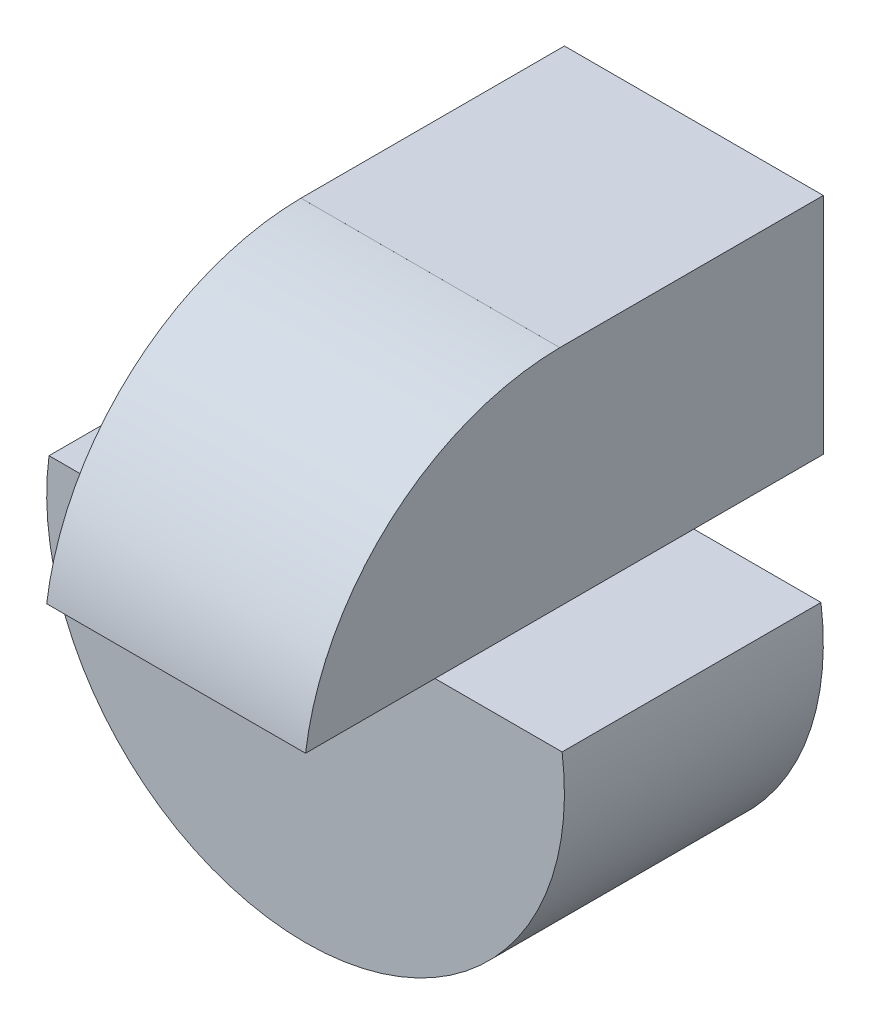
SolidWorks part; units mm, degrees
ref_plane "Front Plane" through (0, 0, 0) normal (0, 0, 1) x (1, 0, 0)
ref_plane "Top Plane" through (0, 0, 0) normal (0, 1, 0) x (1, 0, 0)
ref_plane "Right Plane" through (0, 0, 0) normal (1, 0, 0) x (0, 0, -1)
sketch "Sketch1" plane through (0, 0, 0) normal (0, 0, 1) x (1, 0, 0)
  line L1 (0, 0) -> (40, 0)
  line L2 (0, 0) -> (0, 40)
  line L3 (0, 40) -> (40, 40)
  line L4 (40, 0) -> (40, 40)
  dimension "D1" = 40
  dimension "D2" = 40
extrude "Boss-Extrude1" add sketch "Sketch1" along normal blind 40
sketch "Sketch2" plane through (0, 0, 40) normal (0, 0, 1) x (1, 0, 0)
  line L0 (0, 0) -> (40, 0) construction
  line L1 (0, 40) -> (10, 40)
  line L2 (0, 40) -> (0, 20)
  line L3 (0, 20) -> (10, 20)
  line L4 (10, 40) -> (10, 20)
  line L5 (40, 40) -> (30, 40)
  line L6 (40, 40) -> (40, 20)
  line L7 (40, 20) -> (30, 20)
  line L8 (30, 40) -> (30, 20)
  line L9 (0, 20) -> (0, 0)
  line L10 (0, 0) -> (40, 0)
  line L11 (40, 0) -> (40, 20)
  arc A0 (20, 0) -> (40, 20) centre (20, 20) ccw
  arc A1 (20, 0) -> (0, 20) centre (20, 20) cw
  line M1 (0, 40) -> (0, 0)
  line M2 (0, 0) -> (40, 0)
  line M3 (40, 0) -> (40, 40)
  line M4 (40, 40) -> (0, 40)
  dimension "D5" = 20
  dimension "D6" = 20
  dimension "D1" = 10
  dimension "D2" = 10
  dimension "D3" = 20
  dimension "D4" = 20
extrude "Cut-Extrude1" cut sketch "Sketch2" against normal blind 40 contours A1 M2 M1 | A0 L10 M3 | L8 L7 M4 M3 | L4 L3 M4 M1
sketch "Sketch3" plane through (0, 20, 0) normal (0, 1, 0) x (1, 0, 0)
  line L0 (10, 0) -> (10, -40) construction
  line L1 (0, 0) -> (10, 0)
  line L2 (0, 0) -> (0, -10)
  line L3 (0, -10) -> (10, -10)
  line L4 (10, 0) -> (10, -10)
  line L5 (30, 0) -> (30, -40) construction
  line L6 (40, 0) -> (30, 0)
  line L7 (40, 0) -> (40, -10)
  line L8 (40, -10) -> (30, -10)
  line L9 (30, 0) -> (30, -10)
  line L11 (40, -40) -> (30, -40)
  line L12 (40, -40) -> (40, -30)
  line L13 (40, -30) -> (30, -30)
  line L14 (30, -40) -> (30, -30)
  line L15 (0, -40) -> (10, -40)
  line L16 (0, -40) -> (0, -30)
  line L17 (0, -30) -> (10, -30)
  line L18 (10, -40) -> (10, -30)
  dimension "D1" = 10
  dimension "D2" = 10
  dimension "D3" = 10
  dimension "D4" = 10
extrude "Cut-Extrude2" cut sketch "Sketch3" against normal blind 40
sketch "Sketch4" plane through (10, 0, 0) normal (-1, 0, 0) x (0, 0, 1)
  line L0 (0, 22.6795) -> (10, 22.6795)
  line L1 (0, 2.6795) -> (10, 2.6795)
  line L2 (0, 2.6795) -> (0, 22.6795)
  line L3 (10, 22.6795) -> (10, 20)
  line L4 (10, 2.6795) -> (10, 20)
  line L5 (40, 2.6795) -> (30, 2.6795)
  line L6 (40, 2.6795) -> (40, 22.6795)
  line L7 (40, 22.6795) -> (30, 22.6795)
  line L8 (30, 2.6795) -> (30, 20)
  line L10 (30, 22.6795) -> (30, 20)
  line L12 (10, 20) -> (30, 20) construction
  line L13 (20, 39.9992) -> (40, 40)
  line L14 (40, 40) -> (40, 22.6795)
  arc A0 (40, 22.6795) -> (20, 39.9992) centre (20.1803, 20) ccw
  line M1 (40, 2.6795) -> (40, 40)
  line M3 (0, 40) -> (0, 2.6795)
  line M4 (0, 2.6795) -> (10, 2.6795)
  line M5 (10, 2.6795) -> (10, 20)
  line M7 (30, 20) -> (30, 2.6795)
  line M8 (30, 2.6795) -> (40, 2.6795)
  dimension "D3" = 20
  dimension "D1" = 20
  dimension "D2" = 20
  dimension "D4" = 0
  dimension "D5" = 20
  dimension "D6" = 20
extrude "Cut-Extrude3" cut sketch "Sketch4" against normal blind 40 contours L3 L0 M3 M4 M5 | L7 L10 M7 M8 M1 | A0 L13 M1
sketch "Sketch5" plane through (0, 2.6795, 0) normal (0, 1, 0) x (1, 0, 0)
  line L1 (30, -10) -> (10, -10)
  line L2 (30, -10) -> (30, 0)
  line L3 (30, 0) -> (10, 0)
  line L4 (10, -10) -> (10, 0)
  line L5 (30, -30) -> (10, -30)
  line L6 (30, -30) -> (30, -40)
  line L7 (30, -40) -> (10, -40)
  line L8 (10, -30) -> (10, -40)
extrude "Cut-Extrude4" cut sketch "Sketch5" against normal blind 40
sketch "Sketch6" plane through (0, 39.9984, -0.0016) normal (0, -1, 0) x (1, 0, 0)
  line L1 (30, 40.0016) -> (10, 40.0016)
  line L2 (30, 40.0016) -> (30, 20.3606)
  line L3 (30, 20.3606) -> (10, 20.3606)
  line L4 (10, 40.0016) -> (10, 20.3606)
extrude "Cut-Extrude5" cut sketch "Sketch6" against normal blind 40
sketch "Sketch8" plane through (0, 0, 30) normal (0, 0, 1) x (1, 0, 0)
  line L0 (0.1803, 22.6795) -> (39.8197, 22.6795)
  arc A0 (0.1803, 22.6795) -> (39.8197, 22.6795) centre (20, 20) ccw
  arc A1 (0, 20) -> (40, 20) centre (20, 20) ccw construction
  dimension "D1" = 10
  dimension "D2" = 10
extrude "Boss-Extrude2" add sketch "Sketch8" against normal blind 20
